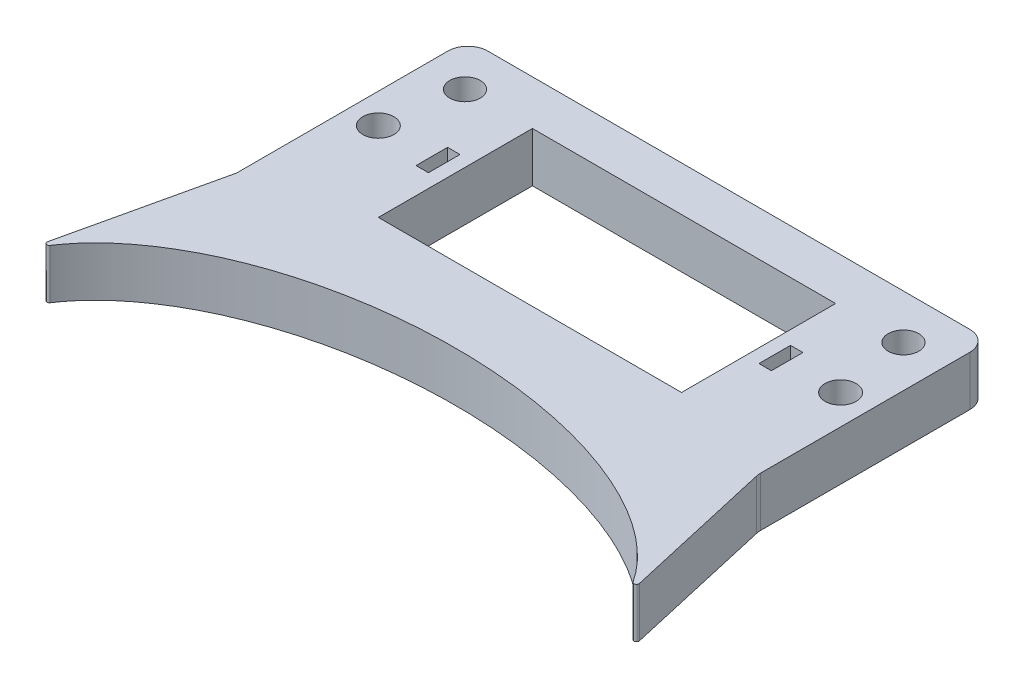
SolidWorks part; units mm, degrees
ref_plane "Front Plane" through (0, 0, 0) normal (0, 0, 1) x (1, 0, 0)
ref_plane "Top Plane" through (0, 0, 0) normal (0, 1, 0) x (1, 0, 0)
ref_plane "Right Plane" through (0, 0, 0) normal (1, 0, 0) x (0, 0, -1)
sketch "Sketch1" plane through (0, 0, 0) normal (0, 1, 0) x (1, 0, 0)
  line L1 (-52.5, -27.5) -> (52.5, -27.5)
  line L2 (-52.5, -27.5) -> (-52.5, 27.5)
  line L3 (-52.5, 27.5) -> (52.5, 27.5)
  line L4 (52.5, -27.5) -> (52.5, 27.5)
  line L5 (0, 27.5) -> (0, -27.5) construction
  line L6 (-52.5, 0) -> (52.5, 0) construction
  point P0 (0, 0)
  dimension "D1" = 105
  dimension "D2" = 55
extrude "Boss-Extrude1" add sketch "Sketch1" along normal blind 10
sketch "Sketch2" plane through (0, 10, 0) normal (0, 1, 0) x (1, 0, 0)
  line L6 (-30.5, 18.5) -> (30.5, 18.5)
  line L7 (-30.5, 18.5) -> (-30.5, -12.5)
  line L8 (-30.5, -12.5) -> (30.5, -12.5)
  line L9 (30.5, 18.5) -> (30.5, -12.5)
  line L10 (0, -12.5) -> (0, 18.5) construction
  line L11 (-30.5, 3) -> (30.5, 3) construction
  line L12 (0, 0) -> (0, -12.5) construction
  line L14 (-52.5, -27.5) -> (52.5, -27.5) construction
  point P0 (0, 3)
  dimension "D1" = 31
  dimension "D2" = 61
  dimension "D3" = 15
extrude "Cut-Extrude1" cut sketch "Sketch2" against normal through all
sketch "Sketch4" plane through (0, 10, 0) normal (0, 1, 0) x (1, 0, 0)
  line L2 (-46.5, 3.5) -> (-34.5, 3.5) construction
  line L3 (30.5, 18.5) -> (-30.5, 18.5) construction
  line L4 (-33.25, 6.675) -> (-35.75, 6.675)
  line L5 (-33.25, 6.675) -> (-33.25, 0.325)
  line L6 (-33.25, 0.325) -> (-35.75, 0.325)
  line L7 (-35.75, 6.675) -> (-35.75, 0.325)
  line L8 (-34.5, 0.325) -> (-34.5, 6.675) construction
  line L9 (-33.25, 3.5) -> (-35.75, 3.5) construction
  line L10 (-30.5, 18.5) -> (-30.5, -12.5) construction
  circle A0 centre (-46.5, 3.5) radius 3.125
  dimension "D1" = 6.25
  dimension "D2" = 15
  dimension "D3" = 16
  dimension "D4" = 2.5
  dimension "D5" = 6.35
  dimension "D6" = 2.75
extrude "Cut-Extrude3" cut sketch "Sketch4" against normal through all
sketch "Sketch5" plane through (0, 0, 0) normal (0, 1, 0) x (1, 0, 0)
  line L0 (0, 0) -> (0, -62.5) construction
  line L1 (-52.5, -27.5) -> (52.5, -27.5) construction
  line L2 (-52.5, -19.0391) -> (-60.2822, -53.2591)
  line L3 (-52.5, 27.5) -> (-52.5, -27.5) construction
  line L4 (-52.5, -19.0391) -> (0, -27.5)
  ellipse E0 centre (0, -62.5) end of major axis (-62.5, -62.5) minor radius 35
  dimension "D1" = 125
  dimension "D2" = 62.5
extrude "Boss-Extrude2" add sketch "Sketch5" along normal up to surface (10 mm away) contours E0 L4 L2 up to face at (-46.5, 10, -0.375)
sketch "Sketch6" plane through (0, 10, 0) normal (0, 1, 0) x (1, 0, 0)
  circle A0 centre (-44.1085, 18.5417) radius 3.075
  dimension "D1" = 6.15
extrude "Cut-Extrude4" cut sketch "Sketch6" against normal through all
mirror "Mirror1" about plane through (0, 0, 0) normal (1, 0, 0) of "Cut-Extrude4", "Boss-Extrude2", "Cut-Extrude3"
fillet "Fillet1" radius 4 4 edges at (-52.5, 5, 19.0391) (52.5, 5, 19.0391) (52.5, 5, -27.5) (-52.5, 5, -27.5)
fillet "Fillet2" radius 0.5 2 edges at (60.2822, 5, 53.2591) (-60.2822, 5, 53.2591)
